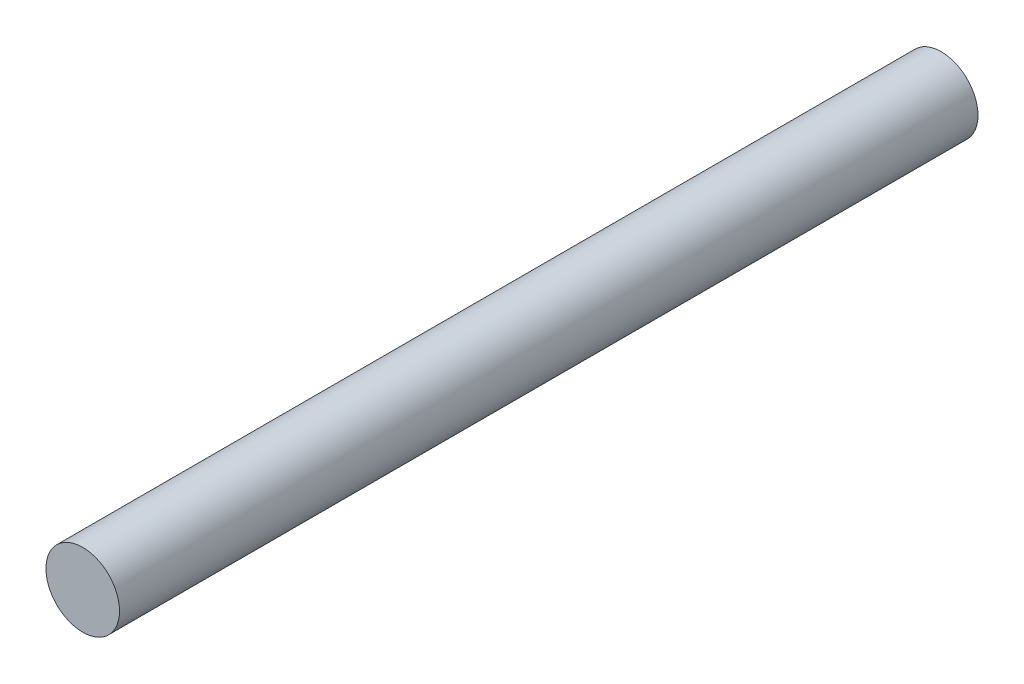
SolidWorks part; units mm, degrees
ref_plane "Front Plane" through (0, 0, 0) normal (0, 0, 1) x (1, 0, 0)
ref_plane "Top Plane" through (0, 0, 0) normal (0, 1, 0) x (1, 0, 0)
ref_plane "Right Plane" through (0, 0, 0) normal (1, 0, 0) x (0, 0, -1)
sketch "Sketch1" plane through (0, 0, 0) normal (0, 0, 1) x (1, 0, 0)
  circle A0 centre (0, 0) radius 3
  dimension "D1" = 6
extrude "Boss-Extrude1" add sketch "Sketch1" along normal blind 70
